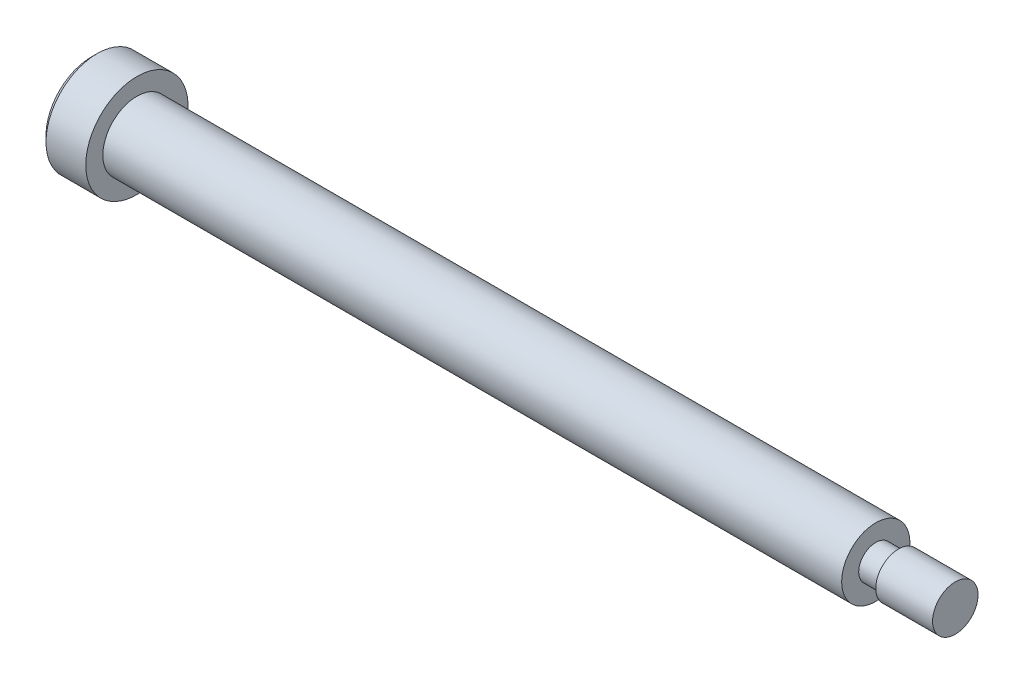
SolidWorks part; units mm, degrees
material "Plain Carbon Steel"
ref_plane "Front Plane" through (0, 0, 0) normal (0, 0, 1) x (1, 0, 0)
ref_plane "Top Plane" through (0, 0, 0) normal (0, 1, 0) x (1, 0, 0)
ref_plane "Right Plane" through (0, 0, 0) normal (1, 0, 0) x (0, 0, -1)
sketch "Sketch1" plane through (0, 0, 0) normal (0, 0, 1) x (1, 0, 0)
  line L0 (0, 3) -> (65, 3)
  line L1 (65, 3) -> (65, 1.5)
  line L2 (65, 1.5) -> (67, 1.5)
  line L3 (67, 1.5) -> (67, 2)
  line L4 (67, 2) -> (72, 2)
  line L5 (72, 2) -> (72, 0)
  line L6 (72, 0) -> (-4, 0)
  line L7 (-4, 0) -> (-4, 4.5)
  line L8 (-4, 4.5) -> (0, 4.5)
  line L9 (0, 4.5) -> (0, 3)
  line L10 (-15.4482, 0) -> (78.4971, 0) construction
  dimension "D1" = 4
  dimension "D2" = 6
  dimension "D3" = 65
  dimension "D4" = 3
  dimension "D5" = 7
  dimension "D6" = 2
  dimension "D7" = 9
  dimension "D8" = 4
revolve "Revolve1" add sketch "Sketch1" angle 360 about L10
cosmetic thread "Cosmetic Thread1" parameters "D2"=3.22
chamfer "Chamfer2" distance 0.5 angle 45 1 edges at (-4, 0, 4.5)
sketch "Sketch2" plane through (-4, 0, 0) normal (-1, 0, 0) x (0, 0, 1)
  line L0 (0, 0) -> (0, 1.7321) construction
  line L1 (0, 1.7321) -> (-1.5, 0.866)
  line L2 (-1.5, 0.866) -> (-1.5, -0.866)
  line L3 (-1.5, -0.866) -> (0, -1.7321)
  line L4 (0, -1.7321) -> (1.5, -0.866)
  line L5 (1.5, -0.866) -> (1.5, 0.866)
  line L6 (1.5, 0.866) -> (0, 1.7321)
  line L7 (0, 1.7321) -> (0.0181, 1.7917) construction
  circle A0 centre (0, 0) radius 1.5 construction
  dimension "D1" = 3
extrude "Cut-Extrude1" cut sketch "Sketch2" against normal blind 2
